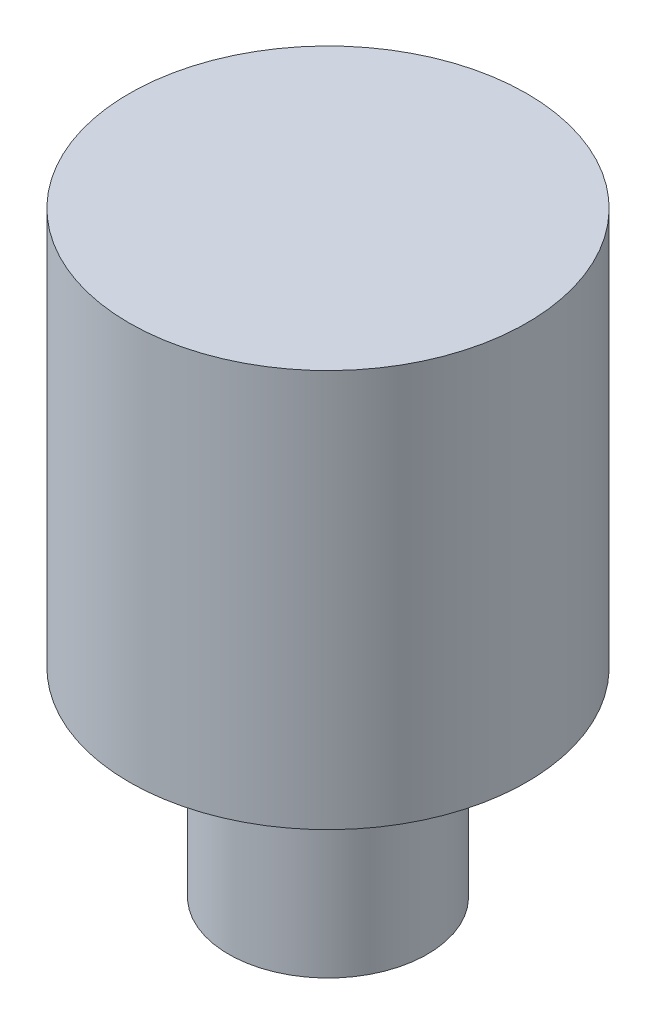
SolidWorks part; units mm, degrees
material "Cast Alloy Steel"
ref_plane "Front Plane" through (0, 0, 0) normal (0, 0, 1) x (1, 0, 0)
ref_plane "Top Plane" through (0, 0, 0) normal (0, 1, 0) x (1, 0, 0)
ref_plane "Right Plane" through (0, 0, 0) normal (1, 0, 0) x (0, 0, -1)
sketch "Sketch1" plane through (0, 0, 0) normal (0, 0, 1) x (1, 0, 0)
  line L0 (0, 0) -> (0, 25.7044) construction
  line L1 (0, 0) -> (2, 0)
  line L2 (0, 0) -> (0, 6)
  line L3 (0, 6) -> (2, 6)
  line L4 (2, 0) -> (2, 6)
  dimension "D1" = 4
  dimension "D2" = 6
revolve "Revolve1" add sketch "Sketch1" angle 360 about L0
sketch "Sketch2" plane through (0, 0, 0) normal (0, 0, 1) x (1, 0, 0)
  line L0 (2, 0) -> (2, 6) construction
  line L1 (1, 0) -> (2, 0)
  line L2 (1, 0) -> (1, 2)
  line L3 (1, 2) -> (2, 2)
  line L4 (2, 0) -> (2, 2)
  line L5 (0, 0) -> (0, 3.6611) construction
  dimension "D1" = 2
  dimension "D2" = 2
revolve "Cut-Revolve1" cut sketch "Sketch2" angle 360 about L5
